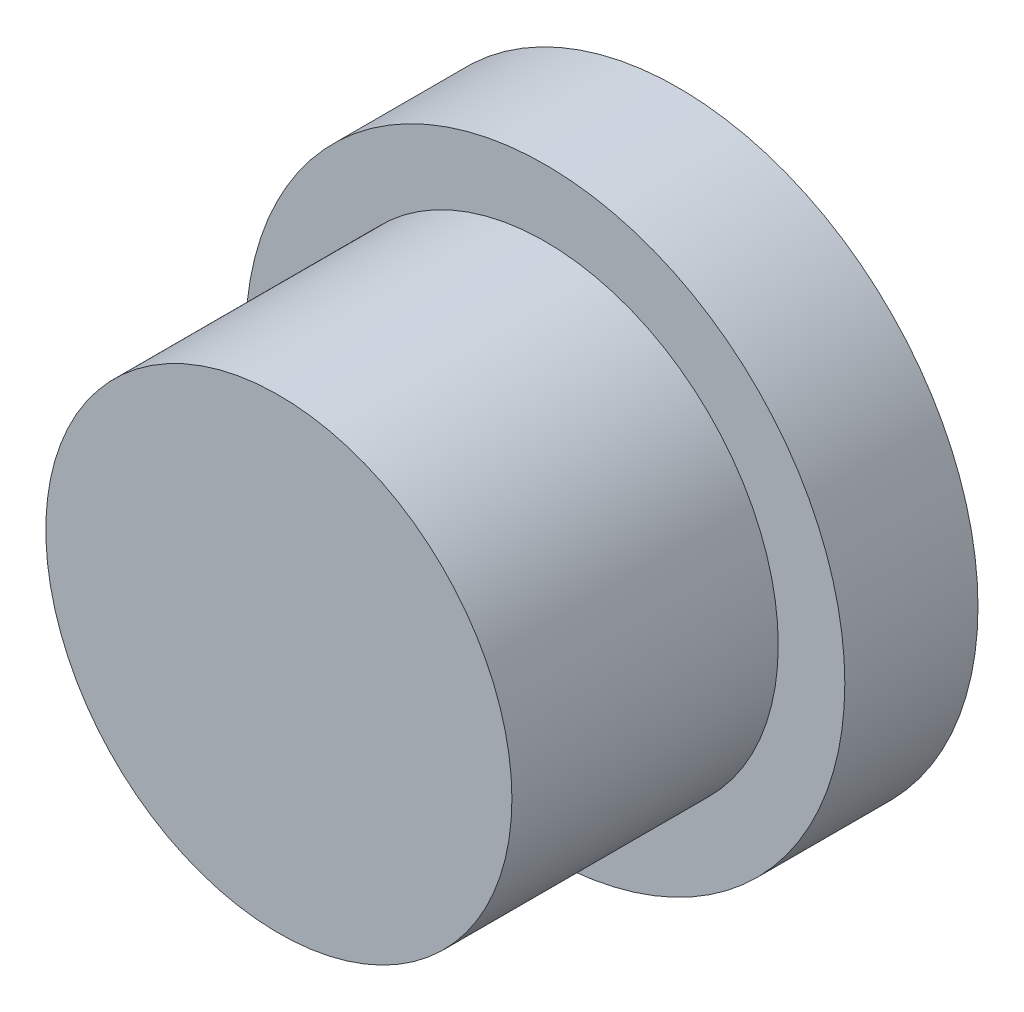
SolidWorks part; units mm, degrees
material "ABS"
ref_plane "Спереди" through (0, 0, 0) normal (0, 0, 1) x (1, 0, 0)
ref_plane "Сверху" through (0, 0, 0) normal (0, 1, 0) x (1, 0, 0)
ref_plane "Справа" through (0, 0, 0) normal (1, 0, 0) x (0, 0, -1)
sketch "Эскиз1" plane through (0, 0, 0) normal (0, 0, 1) x (1, 0, 0)
  circle A0 centre (0, 0) radius 4.5
  dimension "D1" = 9
extrude "Бобышка-Вытянуть1" add sketch "Эскиз1" along normal blind 2 contours A0
sketch "Эскиз2" plane through (0, 0, 2) normal (0, 0, 1) x (1, 0, 0)
  circle A0 centre (0, 0) radius 3.5
  dimension "D1" = 7
extrude "Бобышка-Вытянуть2" add sketch "Эскиз2" along normal blind 4
sketch "Эскиз3" plane through (0, 0, 0) normal (0, 0, -1) x (-1, 0, 0)
  circle A1 centre (0, 0) radius 2.5
  point P6 (0, 0)
  dimension "D1" = 5
extrude "Вырез-Вытянуть1" cut sketch "Эскиз3" against normal blind 5
